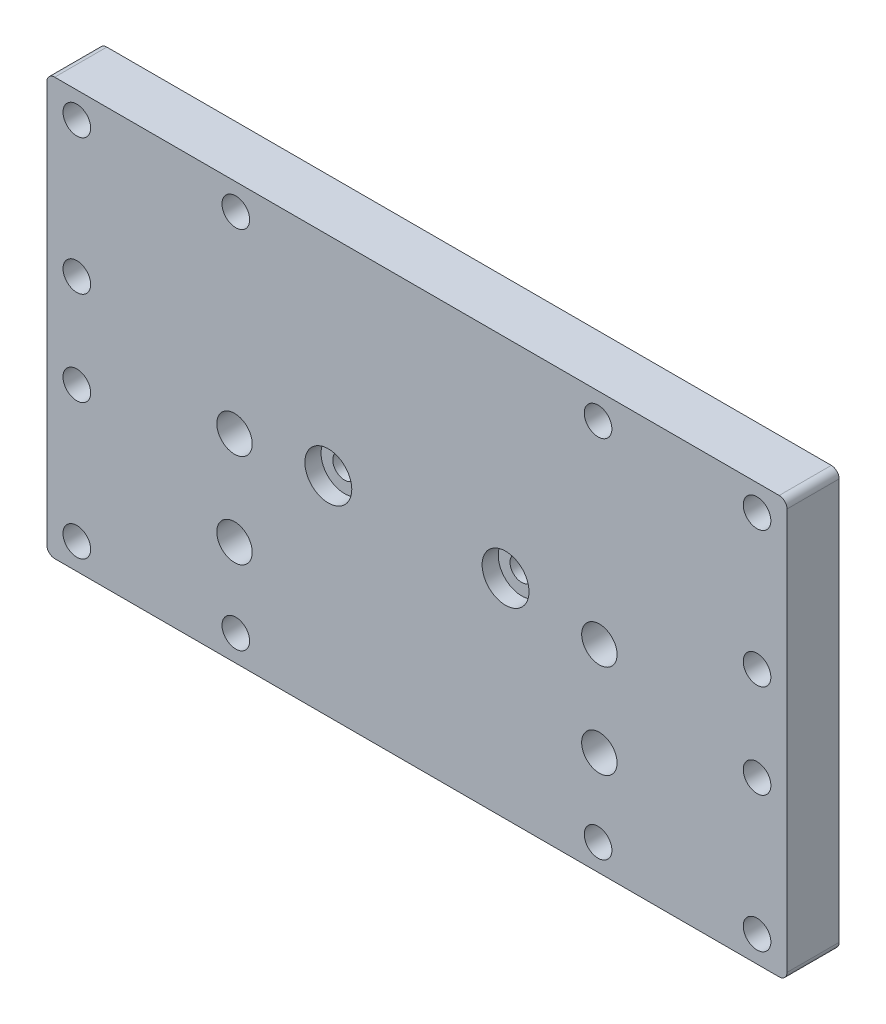
SolidWorks part; units mm, degrees
ref_plane "Front Plane" through (0, 0, 0) normal (0, 0, 1) x (1, 0, 0)
ref_plane "Top Plane" through (0, 0, 0) normal (0, 1, 0) x (1, 0, 0)
ref_plane "Right Plane" through (0, 0, 0) normal (1, 0, 0) x (0, 0, -1)
sketch "Sketch1" plane through (0, 0, 0) normal (0, 0, 1) x (1, 0, 0)
  line L1 (-71, -40) -> (71, -40)
  line L2 (-71, -40) -> (-71, 40)
  line L3 (-71, 40) -> (71, 40)
  line L4 (71, -40) -> (71, 40)
  line L5 (-71, -40) -> (71, 40) construction
  line L6 (-71, 40) -> (71, -40) construction
  point P0 (0, 0)
  dimension "D1" = 80
  dimension "D2" = 142
extrude "Boss-Extrude1" add sketch "Sketch1" along normal mid plane 10
hole_wizard "M5 Clearance Hole1" positions "Sketch6" profile "Sketch5" hole size "M5" standard "ANSI Metric" end condition through all
sketch "Sketch6" plane through (0, 0, 5) normal (0, 0, 1) x (1, 0, 0)
  line L1 (-65.25, 35) -> (-34.75, 35) construction
  line L2 (-65.25, 35) -> (-65.25, 9) construction
  line L3 (-65.25, 9) -> (-34.75, 9) construction
  line L4 (-34.75, 35) -> (-34.75, 9) construction
  line L5 (-65.25, 35) -> (-34.75, 9) construction
  line L6 (-65.25, 9) -> (-34.75, 35) construction
  line L7 (-71, 40) -> (-71, -40) construction
  line L8 (71, 40) -> (-71, 40) construction
  point P0 (-65.25, 35)
  point P2 (-34.75, 35)
  point P4 (-65.25, 9)
  dimension "D1" = 5.75
  dimension "D2" = 5
  dimension "D3" = 26
  dimension "D4" = 30.5
sketch "Sketch5" plane through (-65.25, 35, 5) normal (1, 0, 0) x (0, -1, 0)
  line L0 (0, 0) -> (0, 10)
  line L1 (0, 10) -> (2.65, 10)
  line L2 (2.65, 10) -> (2.65, 0)
  line L5 (2.65, 0) -> (0, 0)
  line L11 (0, -6.35) -> (0, 107.95) construction
  dimension "Thru Hole Dia." = 5.3
  dimension "Thru Hole Depth" = 10
mirror "Mirror1" about plane through (0, 0, 0) normal (1, 0, 0) of "M5 Clearance Hole1"
mirror "Mirror2" about plane through (0, 0, 0) normal (0, 1, 0) of "Mirror1", "M5 Clearance Hole1"
hole_wizard "CBORE for M4 Pan Head Machine Screw1" positions "Sketch8" profile "Sketch7" counterbore size "M4" standard "ANSI Metric" end condition through all
sketch "Sketch8" plane through (-50.3084, 7.5334, 5) normal (0, 0, 1) x (1, 0, 0)
  line L0 (-1000, -7.5334) -> (49000, -7.5334) construction
  point P0 (33.3084, -7.5334)
  point P2 (67.3084, -7.5334)
  dimension "D1" = 17
  dimension "D2" = 17
sketch "Sketch7" plane through (-17, 0, 5) normal (1, 0, 0) x (0, -1, 0)
  line L0 (0, 0) -> (0, 10)
  line L1 (0, 10) -> (2.25, 10)
  line L3 (2.25, 10) -> (2.25, 3.1)
  line L4 (2.25, 3.1) -> (4.5, 3.1)
  line L5 (4.5, 3.1) -> (4.5, 0)
  line L7 (4.5, 0) -> (0, 0)
  line L11 (0, -6.35) -> (0, 107.95) construction
  dimension "Thru Hole Dia." = 4.5
  dimension "Thru Hole Depth" = 10
  dimension "C'Bore Dia." = 9
  dimension "C'Bore Depth" = 3.1
hole_wizard "M8x1.25 Tapped Hole1" positions "Sketch10" profile "Sketch9" tap size "M8x1.25" standard "ANSI Metric" end condition through all
sketch "Sketch10" plane through (0, 0, 5) normal (0, 0, 1) x (1, 0, 0)
  line L1 (-35, -20) -> (35, -20) construction
  line L2 (-35, -20) -> (-35, -2) construction
  line L3 (-35, -2) -> (35, -2) construction
  line L4 (35, -20) -> (35, -2) construction
  line L5 (-35, -20) -> (35, -2) construction
  line L6 (-35, -2) -> (35, -20) construction
  line L7 (-71, -40) -> (71, -40) construction
  point P0 (-35, -2)
  point P2 (35, -2)
  point P4 (35, -20)
  point P6 (-35, -20)
  dimension "D1" = 70
  dimension "D2" = 35
  dimension "D3" = 20
  dimension "D4" = 18
sketch "Sketch9" plane through (-35, -2, 5) normal (1, 0, 0) x (0, -1, 0)
  line L0 (0, 0) -> (0, 10)
  line L1 (0, 10) -> (3.4, 10)
  line L2 (3.4, 10) -> (3.4, 0)
  line L5 (3.4, 0) -> (0, 0)
  line L11 (0, -6.35) -> (0, 107.95) construction
  dimension "Thru Tap Drill Dia." = 6.8
  dimension "Thru Tap Drill Depth" = 10
cosmetic thread "Hole Thread1" parameters "D2"=8
cosmetic thread "Hole Thread2" parameters "D2"=8
cosmetic thread "Hole Thread3" parameters "D2"=8
cosmetic thread "Hole Thread4" parameters "D2"=8
fillet "Fillet1" radius 1.5 4 edges at (-71, -40, 0) (71, -40, 0) (71, 40, 0) (-71, 40, 0)
